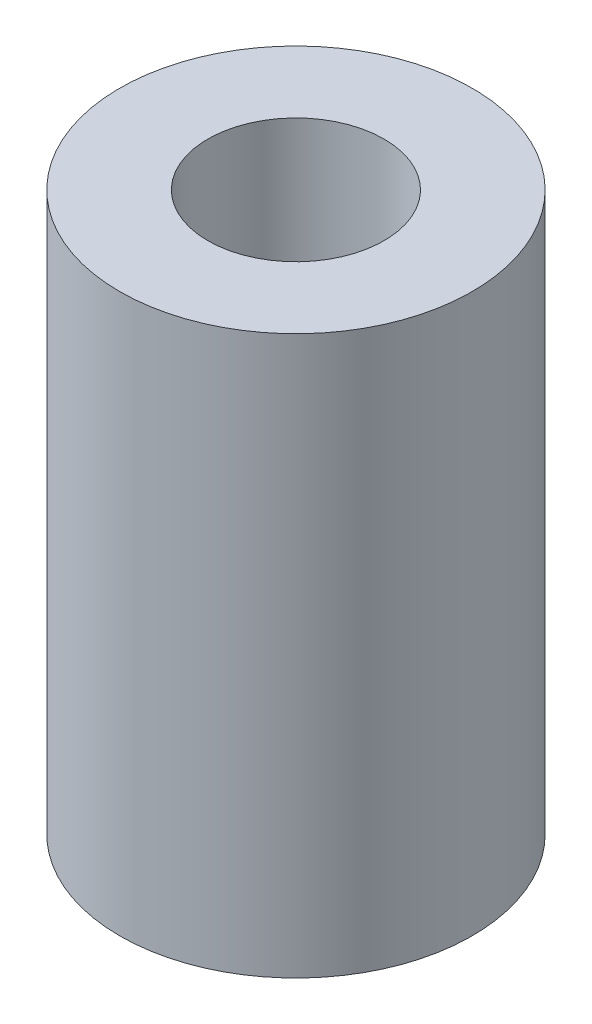
SolidWorks part; units mm, degrees
ref_plane "Front Plane" through (0, 0, 0) normal (0, 0, 1) x (1, 0, 0)
ref_plane "Top Plane" through (0, 0, 0) normal (0, 1, 0) x (1, 0, 0)
ref_plane "Right Plane" through (0, 0, 0) normal (1, 0, 0) x (0, 0, -1)
sketch "Sketch1" plane through (0, 0, 0) normal (0, 1, 0) x (1, 0, 0)
  circle A0 centre (0, 0) radius 6
  circle A1 centre (0, 0) radius 3
extrude "Boss-Extrude1" add sketch "Sketch1" along normal blind 19
